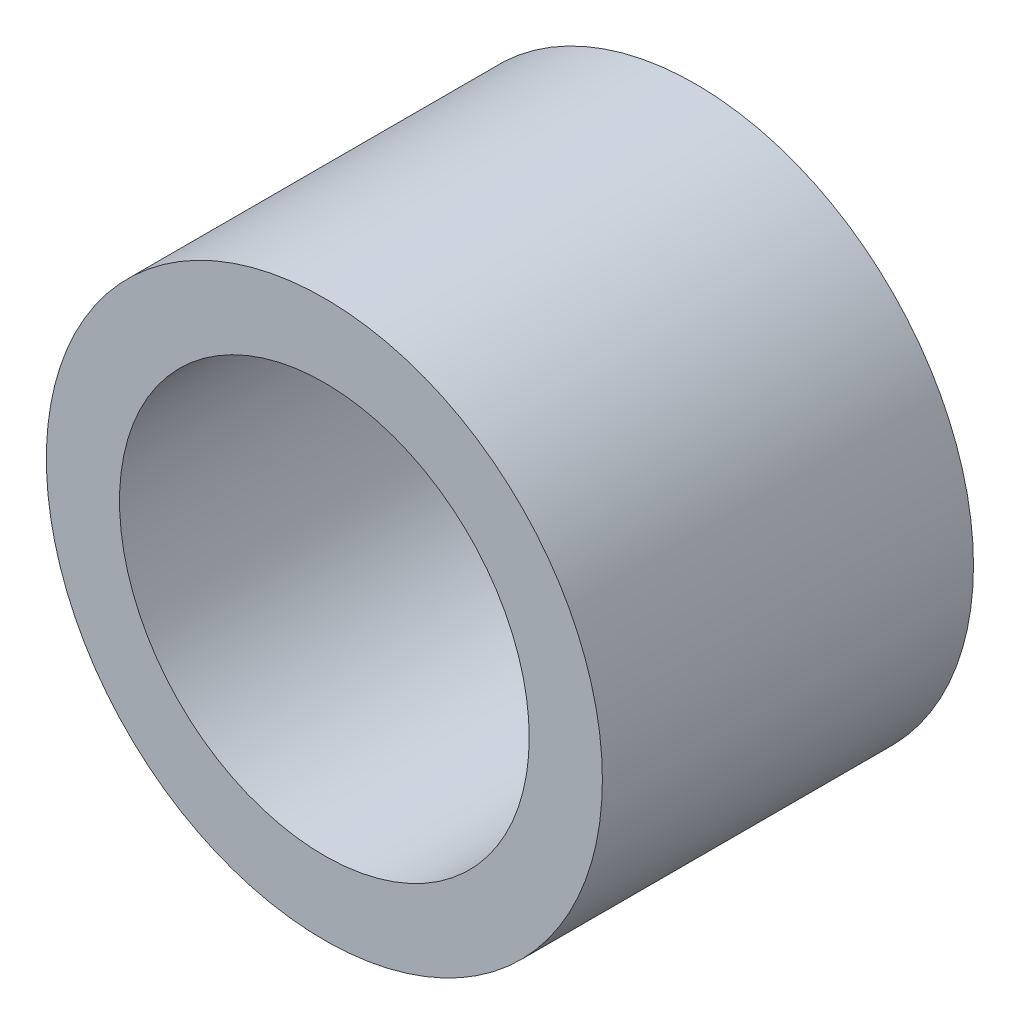
SolidWorks part; units mm, degrees
ref_plane "Front Plane" through (0, 0, 0) normal (0, 0, 1) x (1, 0, 0)
ref_plane "Top Plane" through (0, 0, 0) normal (0, 1, 0) x (1, 0, 0)
ref_plane "Right Plane" through (0, 0, 0) normal (1, 0, 0) x (0, 0, -1)
sketch "Sketch1" plane through (0, 0, 0) normal (0, 0, 1) x (1, 0, 0)
  circle A0 centre (0, 0) radius 4.826
  circle A1 centre (0, 0) radius 3.556
  dimension "D1" = 7.112
  dimension "D2" = 1.27
extrude "Boss-Extrude1" add sketch "Sketch1" along normal blind 6.4414
